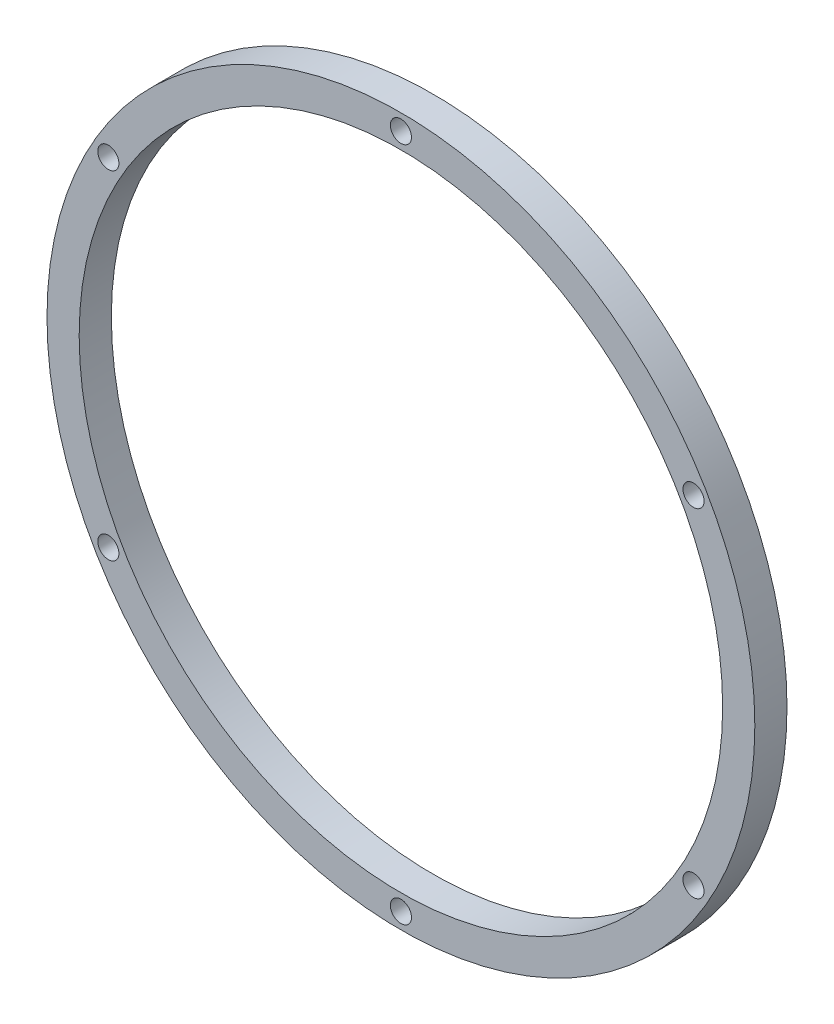
SolidWorks part; units mm, degrees
ref_plane "Front Plane" through (0, 0, 0) normal (0, 0, 1) x (1, 0, 0)
ref_plane "Top Plane" through (0, 0, 0) normal (0, 1, 0) x (1, 0, 0)
ref_plane "Right Plane" through (0, 0, 0) normal (1, 0, 0) x (0, 0, -1)
sketch "Sketch1" plane through (0, 0, 0) normal (0, 0, 1) x (1, 0, 0)
  circle A0 centre (26.6274, 39.8348) radius 69.85
  circle A1 centre (26.6274, 39.8348) radius 63.5
extrude "Boss-Extrude1" add sketch "Sketch1" along normal blind 6.35
sketch "Sketch2" plane through (0, 0, 6.35) normal (0, 0, 1) x (1, 0, 0)
  line L1 (26.6274, 103.3348) -> (26.6274, 109.6848) construction
  circle A0 centre (26.6274, 39.8348) radius 69.85 construction
  circle A1 centre (26.6274, 39.8348) radius 63.5 construction
  circle A2 centre (26.6274, 106.5098) radius 2.085
  circle A3 centre (84.3697, 73.1723) radius 2.085
  circle A4 centre (84.3697, 6.4973) radius 2.085
  circle A5 centre (26.6274, -26.8402) radius 2.085
  circle A6 centre (-31.1148, 6.4973) radius 2.085
  circle A7 centre (-31.1148, 73.1723) radius 2.085
  point P21 (26.6274, 39.8348)
  dimension "D1" = 6
extrude "Cut-Extrude1" cut sketch "Sketch2" against normal blind 21.336
sketch "Sketch3" plane through (0, 0, 6.35) normal (0, 0, 1) x (1, 0, 0)
  line L0 (26.6274, 106.5098) -> (26.6274, 108.5948) construction
  circle A0 centre (26.6274, 106.5098) radius 2.085 construction
  circle A1 centre (26.6274, 106.5098) radius 2.085 construction
